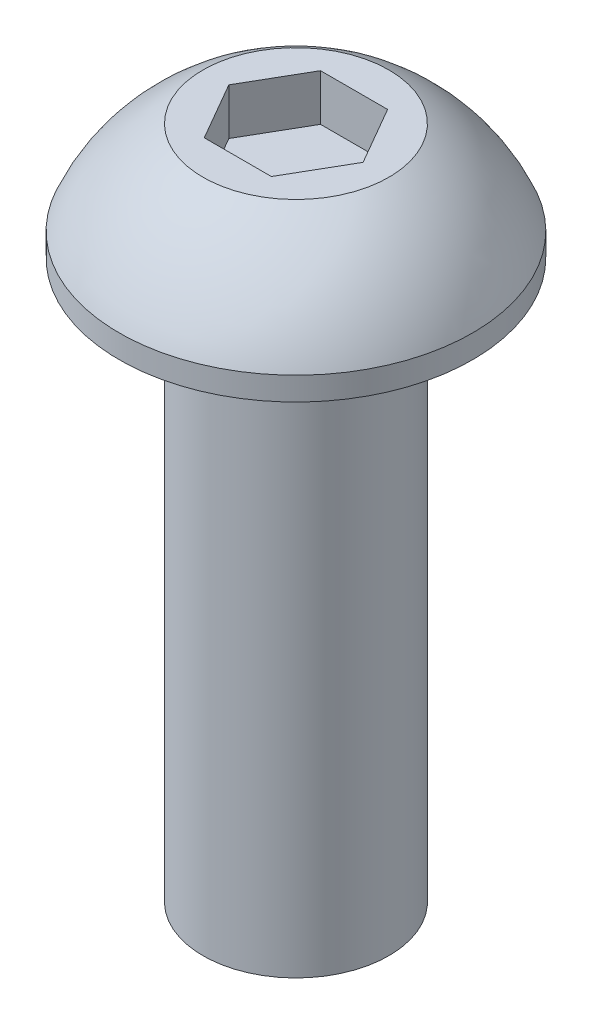
SolidWorks part; units mm, degrees
ref_plane "Front Plane" through (0, 0, 0) normal (0, 0, 1) x (1, 0, 0)
ref_plane "Top Plane" through (0, 0, 0) normal (0, 1, 0) x (1, 0, 0)
ref_plane "Right Plane" through (0, 0, 0) normal (1, 0, 0) x (0, 0, -1)
sketch "Sketch1" plane through (0, 0, 0) normal (0, 0, 1) x (1, 0, 0)
  line L0 (2, 0) -> (3.8, 0)
  line L1 (3.8, 0) -> (3.8, 0.5)
  line L2 (2, 2.5) -> (0, 2.5)
  line L3 (2, 0) -> (2, -12)
  line L4 (2, -12) -> (0, -12)
  line L5 (0, -12) -> (0, 2.5)
  arc A0 (3.8, 0.5) -> (2, 2.5) centre (0.1, -1.02) ccw
  dimension "D5" = 4
  dimension "D1" = 2
  dimension "D2" = 12
  dimension "D3" = 3.8
  dimension "D4" = 2.5
  dimension "D6" = 2
  dimension "D7" = 0.5
revolve "Revolve1" add sketch "Sketch1" angle 360 about L5
sketch "Sketch2" plane through (0, 2.5, 0) normal (0, 1, 0) x (1, 0, 0)
  line L1 (0.7217, 1.25) -> (-0.7217, 1.25)
  line L2 (-0.7217, 1.25) -> (-1.4434, 0)
  line L3 (-1.4434, 0) -> (-0.7217, -1.25)
  line L4 (-0.7217, -1.25) -> (0.7217, -1.25)
  line L5 (0.7217, -1.25) -> (1.4434, 0)
  line L6 (1.4434, 0) -> (0.7217, 1.25)
  circle A0 centre (0, 0) radius 1.25 construction
  dimension "D1" = 2.5
extrude "Cut-Extrude1" cut sketch "Sketch2" against normal blind 1
